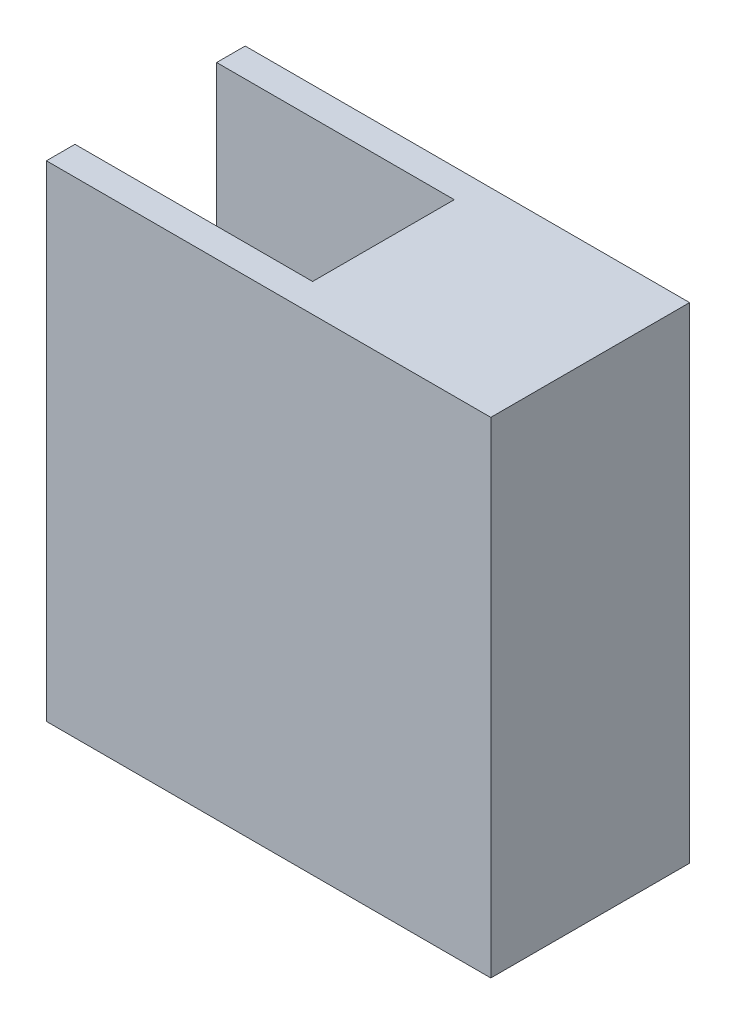
SolidWorks part; units mm, degrees
ref_plane "Front Plane" through (0, 0, 0) normal (0, 0, 1) x (1, 0, 0)
ref_plane "Top Plane" through (0, 0, 0) normal (0, 1, 0) x (1, 0, 0)
ref_plane "Right Plane" through (0, 0, 0) normal (1, 0, 0) x (0, 0, -1)
sketch "Sketch1" plane through (0, 0, 0) normal (1, 0, 0) x (0, 0, -1)
  line L0 (-3.937, -13.4938) -> (-3.937, 11.9062)
  line L1 (5.5245, 13.4937) -> (-5.5245, 13.4937)
  line L2 (5.5245, 13.4937) -> (5.5245, -13.4937)
  line L3 (5.5245, -13.4937) -> (-5.5245, -13.4938)
  line L4 (-5.5245, 13.4937) -> (-5.5245, -13.4938)
  line L5 (5.5245, 13.4937) -> (-5.5245, -13.4938) construction
  line L6 (5.5245, -13.4937) -> (-5.5245, 13.4937) construction
  line L7 (-3.937, 11.9062) -> (3.937, 11.9062)
  line L8 (3.937, 11.9062) -> (3.937, 3.6512)
  line L9 (3.937, 3.6512) -> (0.508, 3.6512)
  line L10 (0.508, 3.6512) -> (0.508, -11.5888)
  line L11 (0.508, -11.5888) -> (-1.651, -11.5888)
  line L12 (-1.651, -11.5888) -> (-1.651, -13.4938)
  line L13 (-1.651, -13.4938) -> (-3.937, -13.4938)
  point P0 (0, 0)
  dimension "D1" = 26.9875
  dimension "D2" = 11.049
  dimension "D3" = 1.5875
  dimension "D4" = 1.5875
  dimension "D5" = 1.5875
  dimension "D6" = 8.255
  dimension "D7" = 4.445
  dimension "D8" = 23.495
  dimension "D9" = 2.286
extrude "Boss-Extrude3" add sketch "Sketch1" along normal mid plane 23.114 contours L11 L12 L3 L2 L1 L4 L0 L7 L8 L9 L10
sketch "Sketch3" plane through (11.557, 0, 0) normal (1, 0, 0) x (0, 0, -1)
  line L1 (-5.5245, 13.4937) -> (5.5245, 13.4937)
  line L2 (-5.5245, 13.4937) -> (-5.5245, -13.4937)
  line L3 (-5.5245, -13.4937) -> (5.5245, -13.4937)
  line L4 (5.5245, 13.4937) -> (5.5245, -13.4937)
extrude "Boss-Extrude4" add sketch "Sketch3" along normal blind 1.5875
sketch "Sketch4" plane through (0, 13.4937, 0) normal (0, 1, 0) x (1, 0, 0)
  line L0 (-11.557, 5.5245) -> (-11.557, -5.5245) construction
  line L1 (-11.557, -3.937) -> (1.651, -3.937)
  line L2 (-11.557, -3.937) -> (-11.557, 3.937)
  line L3 (-11.557, 3.937) -> (1.651, 3.937)
  line L4 (1.651, -3.937) -> (1.651, 3.937)
  line L5 (11.557, -3.937) -> (-11.557, -3.937) construction
  line L6 (11.557, 3.937) -> (-11.557, 3.937) construction
  dimension "D1" = 0
  dimension "D3" = 13.208
extrude "Cut-Extrude1" cut sketch "Sketch4" against normal up to next
